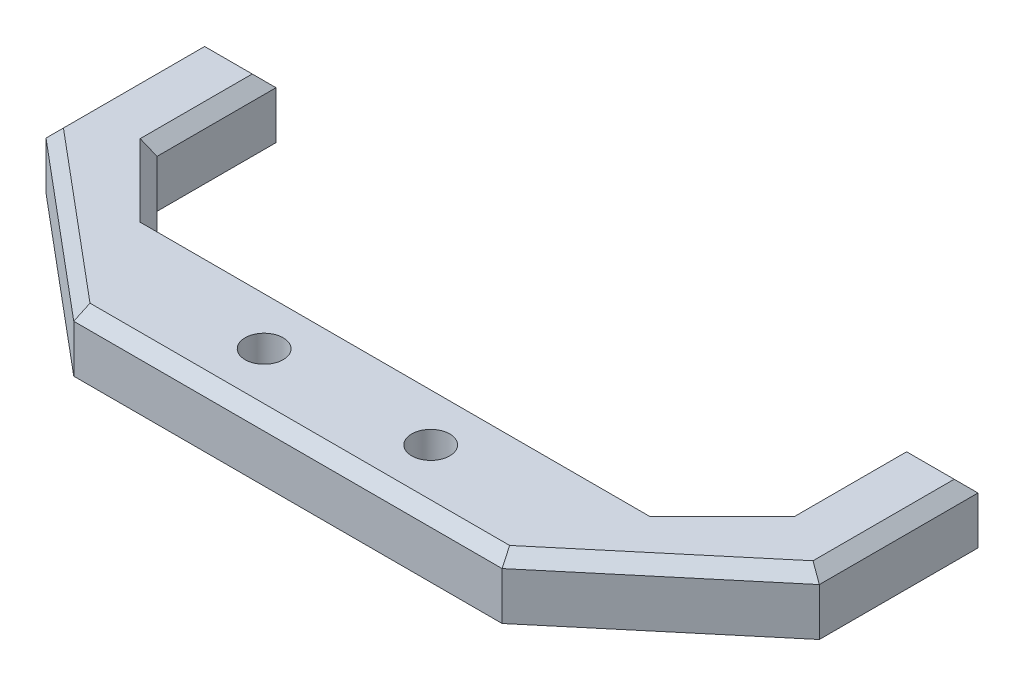
SolidWorks part; units mm, degrees
ref_plane "前视基准面" through (0, 0, 0) normal (0, 0, 1) x (1, 0, 0)
ref_plane "上视基准面" through (0, 0, 0) normal (0, 1, 0) x (1, 0, 0)
ref_plane "右视基准面" through (0, 0, 0) normal (1, 0, 0) x (0, 0, -1)
sketch "草图1" plane through (0, 0, 0) normal (0, 1, 0) x (1, 0, 0)
  line L0 (0, 0) -> (0, -20063.7809) construction
  line L1 (-21, 0) -> (21, 0)
  line L2 (21, 0) -> (26.5, 5.5)
  line L4 (32.5, 2.1669) -> (18, -10)
  line L5 (18, -10) -> (-18, -10)
  line L6 (-32.5, 2.1669) -> (-18, -10)
  line L8 (-21, 0) -> (-26.5, 5.5)
  line L9 (25.5, 74.3238) -> (25.5, 6) construction
  line L10 (25.5, 6) -> (20.5, 1) construction
  line L11 (20.5, 1) -> (-20.5, 1) construction
  line L12 (-20.5, 1) -> (-25.5, 6) construction
  line L13 (-25.5, 6) -> (-25.5, 76.7264) construction
  line L16 (26.5, 5.5) -> (26.5, 15.5)
  line L17 (26.5, 15.5) -> (32.5, 15.5)
  line L19 (-26.5, 15.5) -> (-32.5, 15.5)
  line L20 (-26.5, 5.5) -> (-26.5, 15.5)
  line L21 (32.5, 2.1669) -> (32.5, 15.5)
  line L22 (-32.5, 2.1669) -> (-32.5, 15.5)
  point P10 (0, -10)
  point P13 (0, 0)
  dimension "D1" = 21
  dimension "D2" = 5.5
  dimension "D3" = 135
  dimension "D4" = 18
  dimension "D5" = 10
  dimension "D6" = 140
  dimension "D7" = 45
  dimension "D8" = 10
  dimension "D9" = 51
  dimension "D10" = 25.5
  dimension "D11" = 5
  dimension "D12" = 5
  dimension "D13" = 1
  dimension "D14" = 6
ref_plane "基准面1" through (0, 5, 0) normal (0, 1, 0) x (1, 0, 0)
extrude "凸台-拉伸1" add sketch "草图1" along normal blind 5
sketch "草图7" plane through (0, 5, 0) normal (0, 1, 0) x (1, 0, 0)
  line L0 (0, 0) -> (0, -10) construction
  line L1 (21, 0) -> (-21, 0) construction
  line L2 (-18, -10) -> (18, -10) construction
  line L3 (-24.2759, -5) -> (24.2759, -5) construction
  circle A0 centre (-7, -5) radius 1.6
  circle A1 centre (7, -5) radius 1.6
  point P8 (0, -5)
  dimension "D1" = 3.2
  dimension "D2" = 7
extrude "切除-拉伸1" cut sketch "草图7" against normal through all
chamfer "倒角1" distance 1 angle 45 12 edges at (-25.25, 5, 3.9165) (0, 5, 10) (25.25, 5, 3.9165) (32.5, 5, -8.8335) (29.5, 5, -15.5) (26.5, 5, -10.5) (23.75, 5, -2.75) (0, 5, 0) (-23.75, 5, -2.75) (-26.5, 5, -10.5) (-29.5, 5, -15.5) (-32.5, 5, -8.8335)
